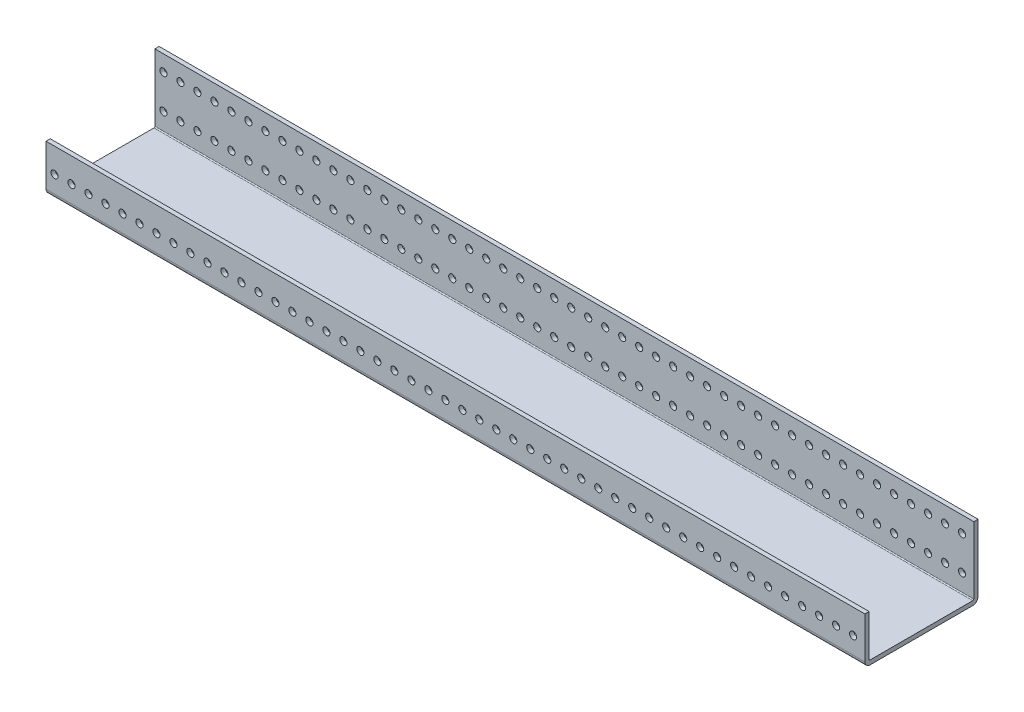
SolidWorks part; units mm, degrees
ref_plane "Front Plane" through (0, 0, 0) normal (0, 0, 1) x (1, 0, 0)
ref_plane "Top Plane" through (0, 0, 0) normal (0, 1, 0) x (1, 0, 0)
ref_plane "Right Plane" through (0, 0, 0) normal (1, 0, 0) x (0, 0, -1)
ref_plane "Plane1" through (0, 34.925, 0) normal (0, 1, 0) x (1, 0, 0)
sketch "Sketch1" plane through (0, 34.925, 0) normal (0, 1, 0) x (1, 0, 0)
  line L0 (685.8, -3.175) -> (685.8, 81.407)
  line L1 (685.8, 81.407) -> (12.7, 81.407)
  line L2 (12.7, 81.407) -> (12.7, -3.175)
  line L3 (12.7, -3.175) -> (685.8, -3.175)
extrude "Boss-Extrude1" add sketch "Sketch1" against normal blind 34.925
sketch "Sketch2" plane through (685.8, 0, 0) normal (1, 0, 0) x (0, 0, -1)
  line L0 (81.407, 34.925) -> (0, 34.925)
  line L1 (0, 34.925) -> (0, 3.175)
  line L2 (0, 3.175) -> (81.407, 3.175)
  line L3 (81.407, 3.175) -> (81.407, 34.925)
extrude "Cut-Extrude1" cut sketch "Sketch2" against normal through all
sketch "Sketch3" plane through (0, 3.175, 0) normal (0, 1, 0) x (-1, 0, 0)
  line L0 (-12.7, -81.407) -> (-685.8, -81.407)
  line L1 (-685.8, -81.407) -> (-685.8, -78.232)
  line L2 (-685.8, -78.232) -> (-12.7, -78.232)
  line L3 (-12.7, -78.232) -> (-12.7, -81.407)
extrude "Boss-Extrude2" add sketch "Sketch3" along normal blind 50.8
hole_wizard "M5 Clearance Hole1" positions "Sketch5" profile "Sketch4" hole size "M5" standard "ANSI Metric"
sketch "Sketch5" plane through (0, 0, -78.232) normal (0, 0, 1) x (1, 0, 0)
  point P0 (679.45, 42.037)
  point P1 (666.75, 42.037)
  point P2 (654.05, 42.037)
  point P3 (641.35, 42.037)
  point P4 (628.65, 42.037)
  point P5 (615.95, 42.037)
  point P6 (603.25, 42.037)
  point P7 (590.55, 42.037)
  point P8 (577.85, 42.037)
  point P9 (565.15, 42.037)
  point P10 (552.45, 42.037)
  point P11 (539.75, 42.037)
  point P12 (527.05, 42.037)
  point P13 (514.35, 42.037)
  point P14 (501.65, 42.037)
  point P15 (488.95, 42.037)
  point P16 (476.25, 42.037)
  point P17 (463.55, 42.037)
  point P18 (450.85, 42.037)
  point P19 (438.15, 42.037)
  point P20 (425.45, 42.037)
  point P21 (412.75, 42.037)
  point P22 (400.05, 42.037)
  point P23 (387.35, 42.037)
  point P24 (374.65, 42.037)
  point P25 (361.95, 42.037)
  point P26 (349.25, 42.037)
  point P27 (336.55, 42.037)
  point P28 (323.85, 42.037)
  point P29 (311.15, 42.037)
  point P30 (298.45, 42.037)
  point P31 (285.75, 42.037)
  point P32 (273.05, 42.037)
  point P33 (260.35, 42.037)
  point P34 (247.65, 42.037)
  point P35 (234.95, 42.037)
  point P36 (222.25, 42.037)
  point P37 (209.55, 42.037)
  point P38 (196.85, 42.037)
  point P39 (184.15, 42.037)
  point P40 (171.45, 42.037)
  point P41 (158.75, 42.037)
  point P42 (146.05, 42.037)
  point P43 (133.35, 42.037)
  point P44 (120.65, 42.037)
  point P45 (107.95, 42.037)
  point P46 (95.25, 42.037)
  point P47 (82.55, 42.037)
  point P48 (69.85, 42.037)
  point P49 (57.15, 42.037)
  point P50 (44.45, 42.037)
  point P51 (31.75, 42.037)
  point P52 (19.05, 42.037)
sketch "Sketch4" plane through (679.45, 42.037, -78.232) normal (1, 0, 0) x (0, -1, 0)
  line L0 (0, 0) -> (0, 3.175)
  line L1 (0, 3.175) -> (2.667, 3.175)
  line L2 (2.667, 3.175) -> (2.667, 0)
  line L5 (2.667, 0) -> (0, 0)
  line L11 (0, -6.35) -> (0, 107.95) construction
  dimension "Thru Hole Dia." = 5.334
  dimension "Thru Hole Depth" = 3.175
hole_wizard "M5 Clearance Hole2" positions "Sketch7" profile "Sketch6" hole size "M5" standard "ANSI Metric"
sketch "Sketch7" plane through (0, 0, 0) normal (0, 0, -1) x (-1, 0, 0)
  point P0 (-679.45, 16.637)
  point P1 (-666.75, 16.637)
  point P2 (-654.05, 16.637)
  point P3 (-641.35, 16.637)
  point P4 (-628.65, 16.637)
  point P5 (-615.95, 16.637)
  point P6 (-603.25, 16.637)
  point P7 (-590.55, 16.637)
  point P8 (-577.85, 16.637)
  point P9 (-565.15, 16.637)
  point P10 (-552.45, 16.637)
  point P11 (-539.75, 16.637)
  point P12 (-527.05, 16.637)
  point P13 (-514.35, 16.637)
  point P14 (-501.65, 16.637)
  point P15 (-488.95, 16.637)
  point P16 (-476.25, 16.637)
  point P17 (-463.55, 16.637)
  point P18 (-450.85, 16.637)
  point P19 (-438.15, 16.637)
  point P20 (-425.45, 16.637)
  point P21 (-412.75, 16.637)
  point P22 (-400.05, 16.637)
  point P23 (-387.35, 16.637)
  point P24 (-374.65, 16.637)
  point P25 (-361.95, 16.637)
  point P26 (-349.25, 16.637)
  point P27 (-336.55, 16.637)
  point P28 (-323.85, 16.637)
  point P29 (-311.15, 16.637)
  point P30 (-298.45, 16.637)
  point P31 (-285.75, 16.637)
  point P32 (-273.05, 16.637)
  point P33 (-260.35, 16.637)
  point P34 (-247.65, 16.637)
  point P35 (-234.95, 16.637)
  point P36 (-222.25, 16.637)
  point P37 (-209.55, 16.637)
  point P38 (-196.85, 16.637)
  point P39 (-184.15, 16.637)
  point P40 (-171.45, 16.637)
  point P41 (-158.75, 16.637)
  point P42 (-146.05, 16.637)
  point P43 (-133.35, 16.637)
  point P44 (-120.65, 16.637)
  point P45 (-107.95, 16.637)
  point P46 (-95.25, 16.637)
  point P47 (-82.55, 16.637)
  point P48 (-69.85, 16.637)
  point P49 (-57.15, 16.637)
  point P50 (-44.45, 16.637)
  point P51 (-31.75, 16.637)
  point P52 (-19.05, 16.637)
sketch "Sketch6" plane through (679.45, 16.637, 0) normal (1, 0, 0) x (0, 1, 0)
  line L0 (0, 0) -> (0, 3.175)
  line L1 (0, 3.175) -> (2.667, 3.175)
  line L2 (2.667, 3.175) -> (2.667, 0)
  line L5 (2.667, 0) -> (0, 0)
  line L11 (0, -6.35) -> (0, 107.95) construction
  dimension "Thru Hole Dia." = 5.334
  dimension "Thru Hole Depth" = 3.175
hole_wizard "M5 Clearance Hole3" positions "Sketch9" profile "Sketch8" hole size "M5" standard "ANSI Metric"
sketch "Sketch9" plane through (0, 0, -81.407) normal (0, 0, -1) x (-1, 0, 0)
  point P0 (-679.45, 16.637)
  point P1 (-666.75, 16.637)
  point P2 (-654.05, 16.637)
  point P3 (-641.35, 16.637)
  point P4 (-628.65, 16.637)
  point P5 (-615.95, 16.637)
  point P6 (-603.25, 16.637)
  point P7 (-590.55, 16.637)
  point P8 (-577.85, 16.637)
  point P9 (-565.15, 16.637)
  point P10 (-552.45, 16.637)
  point P11 (-539.75, 16.637)
  point P12 (-527.05, 16.637)
  point P13 (-514.35, 16.637)
  point P14 (-501.65, 16.637)
  point P15 (-488.95, 16.637)
  point P16 (-476.25, 16.637)
  point P17 (-463.55, 16.637)
  point P18 (-450.85, 16.637)
  point P19 (-438.15, 16.637)
  point P20 (-425.45, 16.637)
  point P21 (-412.75, 16.637)
  point P22 (-400.05, 16.637)
  point P23 (-387.35, 16.637)
  point P24 (-374.65, 16.637)
  point P25 (-361.95, 16.637)
  point P26 (-349.25, 16.637)
  point P27 (-336.55, 16.637)
  point P28 (-323.85, 16.637)
  point P29 (-311.15, 16.637)
  point P30 (-298.45, 16.637)
  point P31 (-285.75, 16.637)
  point P32 (-273.05, 16.637)
  point P33 (-260.35, 16.637)
  point P34 (-247.65, 16.637)
  point P35 (-234.95, 16.637)
  point P36 (-222.25, 16.637)
  point P37 (-209.55, 16.637)
  point P38 (-196.85, 16.637)
  point P39 (-184.15, 16.637)
  point P40 (-171.45, 16.637)
  point P41 (-158.75, 16.637)
  point P42 (-146.05, 16.637)
  point P43 (-133.35, 16.637)
  point P44 (-120.65, 16.637)
  point P45 (-107.95, 16.637)
  point P46 (-95.25, 16.637)
  point P47 (-82.55, 16.637)
  point P48 (-69.85, 16.637)
  point P49 (-57.15, 16.637)
  point P50 (-44.45, 16.637)
  point P51 (-31.75, 16.637)
  point P52 (-19.05, 16.637)
sketch "Sketch8" plane through (679.45, 16.637, -81.407) normal (1, 0, 0) x (0, 1, 0)
  line L0 (0, 0) -> (0, 84.582)
  line L1 (0, 84.582) -> (2.667, 84.582)
  line L2 (2.667, 84.582) -> (2.667, 0)
  line L5 (2.667, 0) -> (0, 0)
  line L11 (0, -6.35) -> (0, 107.95) construction
  dimension "Thru Hole Dia." = 5.334
  dimension "Thru Hole Depth" = 84.582
fillet "Fillet1" radius 0.762 2 edges at (349.25, 3.175, 0) (349.25, 3.175, -78.232)
fillet "Fillet2" radius 3.937 2 edges at (349.25, 0, -81.407) (349.25, 0, 3.175)
sketch "Sketch10" plane through (0, 0, 0) normal (0, -1, 0) x (1, 0, 0)
  line L0 (685.8, -120.7643) -> (624.7, -120.7643)
  line L1 (685.8, -120.7643) -> (685.8, 51.3808)
  line L2 (685.8, 51.3808) -> (624.7, 51.3808)
  line L3 (624.7, -120.7643) -> (624.7, 51.3808)
extrude "Cut-Extrude2" cut sketch "Sketch10" against normal through all
